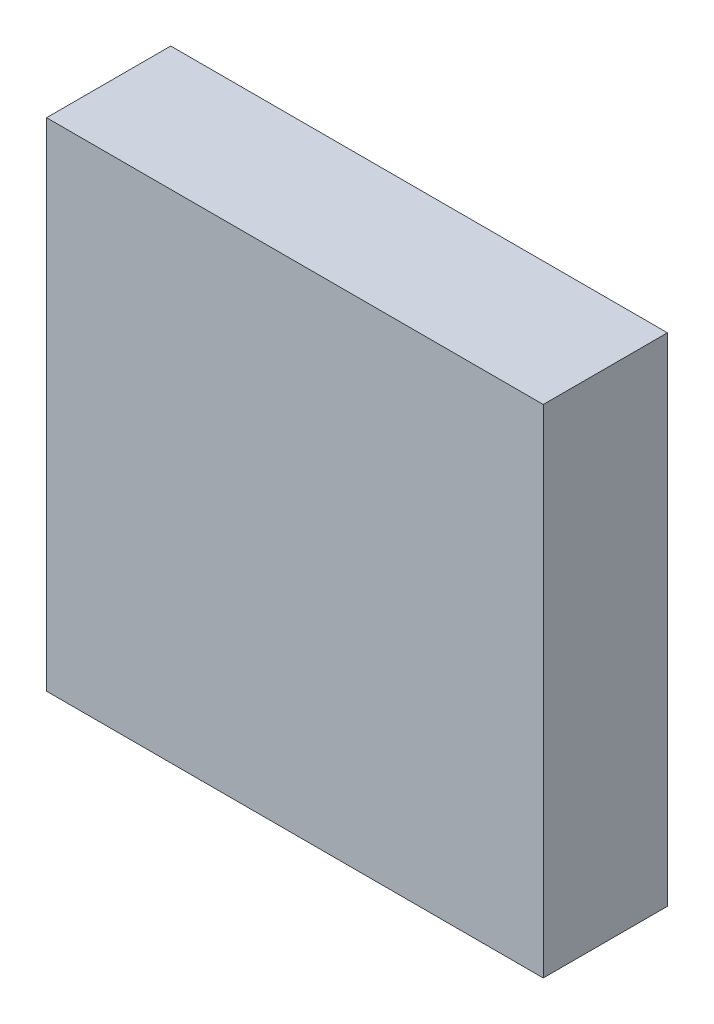
SolidWorks part; units mm, degrees
ref_plane "Alzado" through (0, 0, 0) normal (0, 0, 1) x (1, 0, 0)
ref_plane "Planta" through (0, 0, 0) normal (0, 1, 0) x (1, 0, 0)
ref_plane "Vista lateral" through (0, 0, 0) normal (1, 0, 0) x (0, 0, -1)
sketch "Croquis1" plane through (0, 0, 0) normal (0, 0, 1) x (1, 0, 0)
  line L1 (-20, 20) -> (20, 20)
  line L2 (-20, 20) -> (-20, -20)
  line L3 (-20, -20) -> (20, -20)
  line L4 (20, 20) -> (20, -20)
  line L5 (-20, 20) -> (20, -20) construction
  line L6 (-20, -20) -> (20, 20) construction
  point P0 (0, 0)
extrude "Saliente-Extruir1" add sketch "Croquis1" along normal blind 10
